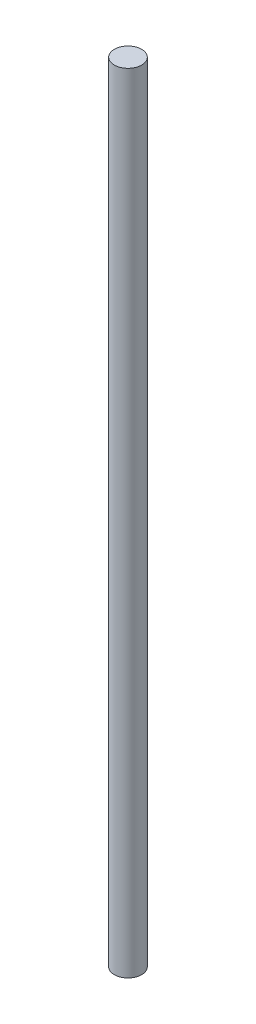
SolidWorks part; units mm, degrees
ref_plane "Front Plane" through (0, 0, 0) normal (0, 0, 1) x (1, 0, 0)
ref_plane "Top Plane" through (0, 0, 0) normal (0, 1, 0) x (1, 0, 0)
ref_plane "Right Plane" through (0, 0, 0) normal (1, 0, 0) x (0, 0, -1)
sketch "Sketch1" plane through (0, 0, 0) normal (0, 1, 0) x (1, 0, 0)
  circle A0 centre (0, 0) radius 3.9688
  dimension "D1" = 7.9375
extrude "Boss-Extrude1" add sketch "Sketch1" along normal blind 228.6
